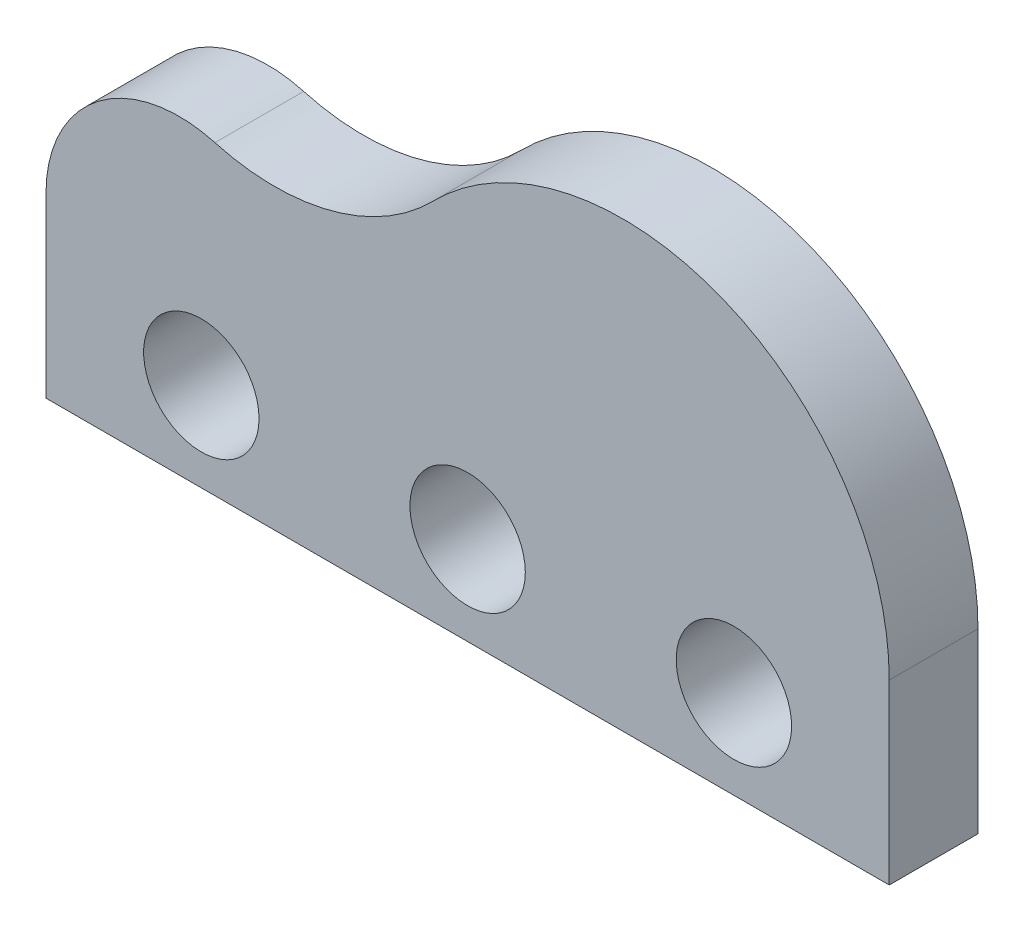
SolidWorks part; units mm, degrees
ref_plane "Front Plane" through (0, 0, 0) normal (0, 0, 1) x (1, 0, 0)
ref_plane "Top Plane" through (0, 0, 0) normal (0, 1, 0) x (1, 0, 0)
ref_plane "Right Plane" through (0, 0, 0) normal (1, 0, 0) x (0, 0, -1)
sketch "Sketch1" plane through (0, 0, 0) normal (0, 0, 1) x (1, 0, 0)
  line L0 (0, 20) -> (0, 0)
  line L1 (0, 0) -> (95, 0)
  line L2 (95, 0) -> (95, 20)
  arc A0 (0, 20) -> (19.0312, 34.4481) centre (15, 20) cw
  arc A1 (19.0312, 34.4481) -> (43.5909, 41.0155) centre (25.75, 58.5284) ccw
  arc A2 (43.5909, 41.0155) -> (95, 20) centre (65, 20) cw
  circle A3 centre (17.5, 10) radius 6.5
  circle A4 centre (47.5, 10) radius 6.5
  circle A5 centre (77.5, 10) radius 6.5
  point P14 (0, 0)
  point P17 (0, 0)
  point P18 (0, 10)
  point P19 (48.5462, 10)
  point P20 (47.5, 0)
  dimension "D3" = 15
  dimension "D4" = 25
  dimension "D5" = 30
  dimension "D8" = 13
  dimension "D1" = 95
  dimension "D2" = 20
  dimension "D6" = 30
  dimension "D7" = 30
extrude "Boss-Extrude1" add sketch "Sketch1" along normal mid plane 10
